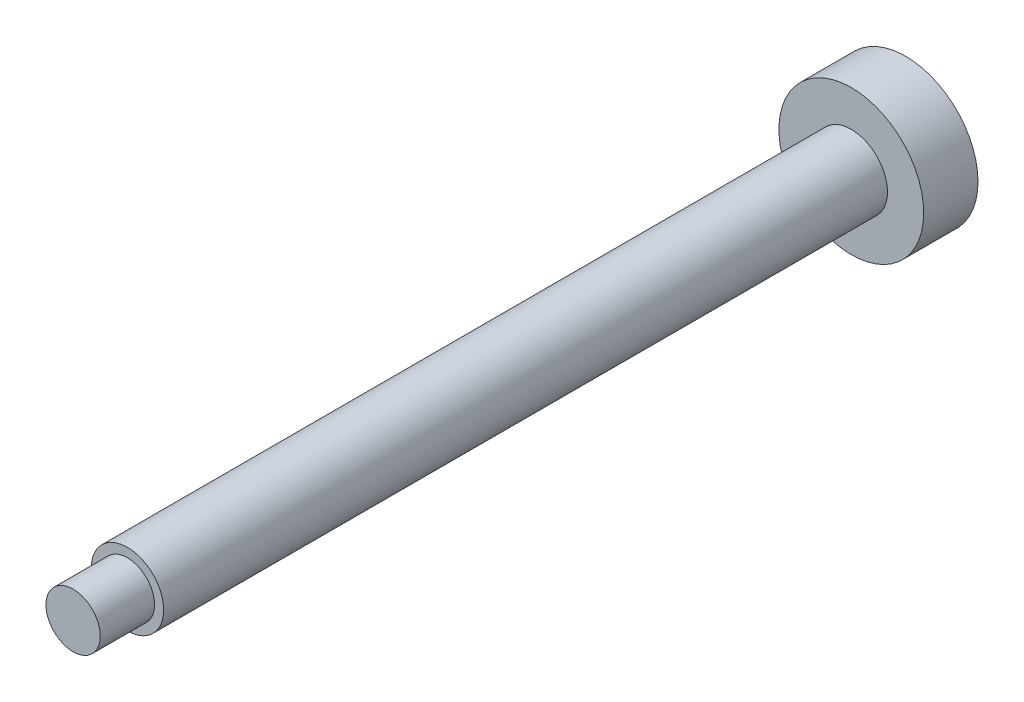
SolidWorks part; units mm, degrees
ref_plane "Front Plane" through (0, 0, 0) normal (0, 0, 1) x (1, 0, 0)
ref_plane "Top Plane" through (0, 0, 0) normal (0, 1, 0) x (1, 0, 0)
ref_plane "Right Plane" through (0, 0, 0) normal (1, 0, 0) x (0, 0, -1)
sketch "Sketch1" plane through (0, 0, 0) normal (0, 0, 1) x (1, 0, 0)
  circle A0 centre (0, 0) radius 2
extrude "Boss-Extrude1" add sketch "Sketch1" along normal blind 40 contours A0
sketch "Sketch3" plane through (0, 0, 0) normal (0, 0, 1) x (1, 0, 0)
  circle A0 centre (0, 0) radius 1.5
extrude "Boss-Extrude2" add sketch "Sketch3" along normal blind 43
sketch "Sketch4" plane through (0, 0, 0) normal (0, 0, 1) x (1, 0, 0)
  circle A0 centre (0, 0) radius 4
extrude "Boss-Extrude3" add sketch "Sketch4" against normal blind 3
